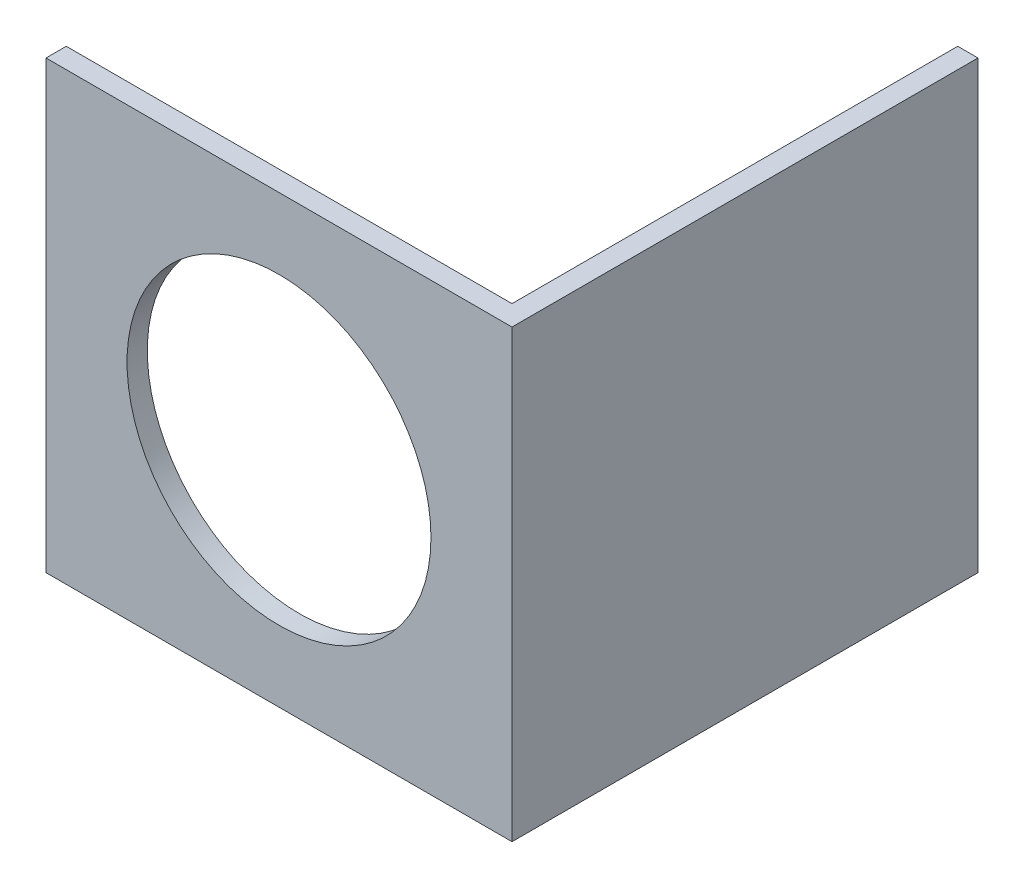
SolidWorks part; units mm, degrees
ref_plane "Front Plane" through (0, 0, 0) normal (0, 0, 1) x (1, 0, 0)
ref_plane "Top Plane" through (0, 0, 0) normal (0, 1, 0) x (1, 0, 0)
ref_plane "Right Plane" through (0, 0, 0) normal (1, 0, 0) x (0, 0, -1)
sketch "Sketch1" plane through (0, 0, 0) normal (0, 1, 0) x (1, 0, 0)
  line L0 (-9.5799, -19.512) -> (36.4201, -19.512)
  line L1 (36.4201, -19.512) -> (36.4201, 26.488)
  line L2 (36.4201, 26.488) -> (34.4201, 26.488)
  line L3 (34.4201, 26.488) -> (34.4201, -17.512)
  line L4 (34.4201, -17.512) -> (-9.5799, -17.512)
  line L5 (-9.5799, -17.512) -> (-9.5799, -19.512)
  dimension "D1" = 2
  dimension "D2" = 2
  dimension "D3" = 46
  dimension "D4" = 46
extrude "Boss-Extrude1" add sketch "Sketch1" along normal blind 44
ref_plane "Plane1" through (0, 0, 19.512) normal (0, 0, 1) x (1, 0, 0)
sketch "Sketch2" plane through (0, 0, 19.512) normal (0, 0, 1) x (1, 0, 0)
  line L0 (-9.5799, 22) -> (36.4201, 22)
  line L1 (-9.5799, 44) -> (-9.5799, 0) construction
  line L2 (36.4201, 44) -> (36.4201, 0) construction
  circle A0 centre (13.4201, 22) radius 15
extrude "Cut-Extrude1" cut sketch "Sketch2" against normal blind 44 contours L0 A0 | L0 A0
